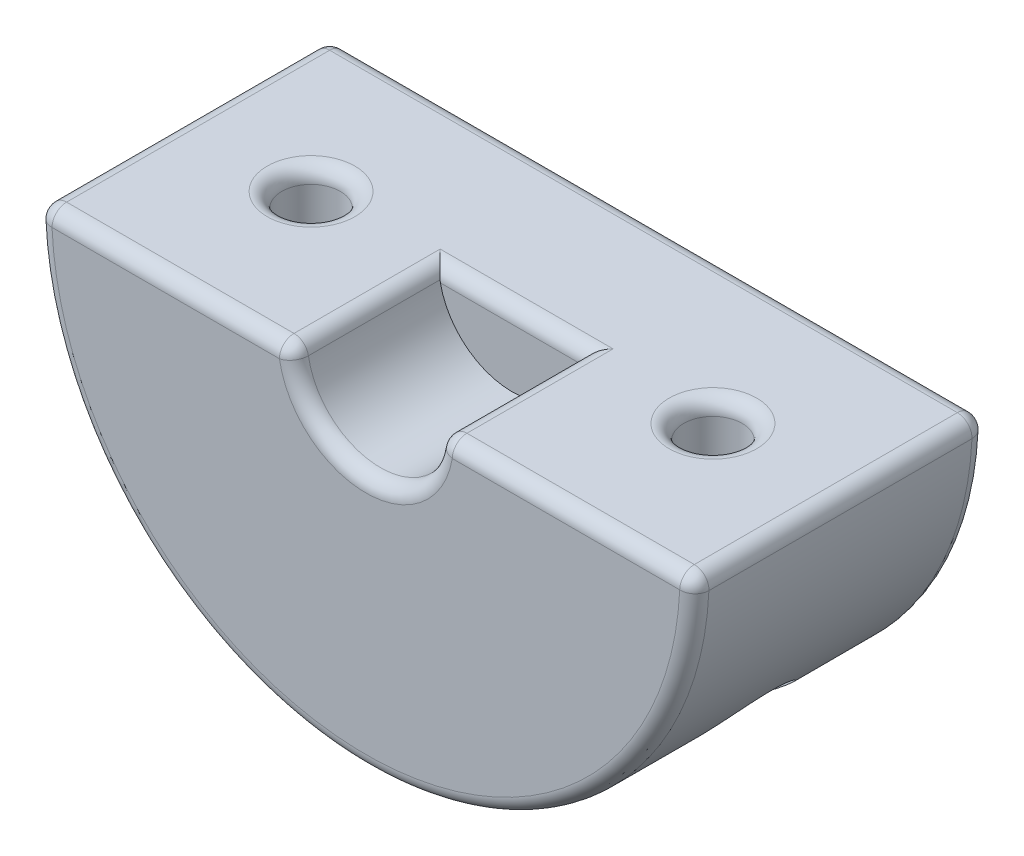
SolidWorks part; units mm, degrees
ref_plane "Front Plane" through (0, 0, 0) normal (0, 0, 1) x (1, 0, 0)
ref_plane "Top Plane" through (0, 0, 0) normal (0, 1, 0) x (1, 0, 0)
ref_plane "Right Plane" through (0, 0, 0) normal (1, 0, 0) x (0, 0, -1)
sketch "Sketch1" plane through (0, 0, 0) normal (0, 0, 1) x (1, 0, 0)
  line L0 (-22.5, 0) -> (22.5, 0)
  arc A0 (-22.5, 0) -> (22.5, 0) centre (0, 0) ccw
  dimension "D1" = 45
extrude "Boss-Extrude1" add sketch "Sketch1" along normal mid plane 20
sketch "Sketch2" plane through (0, 0, 10) normal (0, 0, 1) x (1, 0, 0)
  line L0 (22.5, 0) -> (-22.5, 0) construction
  circle A0 centre (0, 0) radius 5
  dimension "D1" = 10
extrude "Cut-Extrude1" cut sketch "Sketch2" against normal blind 10
sketch "Sketch3" plane through (0, 0, 0) normal (0, 1, 0) x (1, 0, 0)
  line L0 (22.5, -10) -> (22.5, 10) construction
  line L1 (-5, -10) -> (-22.5, -10) construction
  line L2 (22.5, -10) -> (5, -10) construction
  circle A0 centre (13.75, 0) radius 2
  circle A1 centre (-13.75, 0) radius 2
  point P7 (22.5, 0)
  point P11 (-13.75, -10)
  point P14 (13.75, -10)
  dimension "D1" = 4
extrude "Cut-Extrude2" cut sketch "Sketch3" against normal through all
ref_plane "Plane1" through (0, -25, 0) normal (0, 1, 0) x (1, 0, 0)
sketch "Sketch4" plane through (0, -25, 0) normal (0, 1, 0) x (1, 0, 0)
  circle A0 centre (13.75, 0) radius 2 construction
  circle A1 centre (-13.75, 0) radius 2 construction
  circle A2 centre (13.75, 0) radius 2
  circle A3 centre (-13.75, 0) radius 2
  circle A4 centre (13.75, 0) radius 4
  circle A5 centre (-13.75, 0) radius 4
  dimension "D1" = 8
extrude "Cut-Extrude3" cut sketch "Sketch4" along normal blind 12 contours A4 | A5
fillet "Fillet1" radius 1 13 edges at (5, 0, 5) (-5, 0, 5) (-13.75, 0, 10) (13.75, 0, 10) (22.5, 0, 0) (-22.5, 0, 0) (0, 0, -10) (0, 0, 0) (-13.75, 0, 2) (13.75, 0, 2) (0, -5, 10) (0, -22.5, -10) (0, -22.5, 10)
fillet "Fillet2" radius 0.5 4 edges at (-13.75, -13, 4) (-13.75, -13, 2) (13.75, -13, 4) (13.75, -13, 2)
